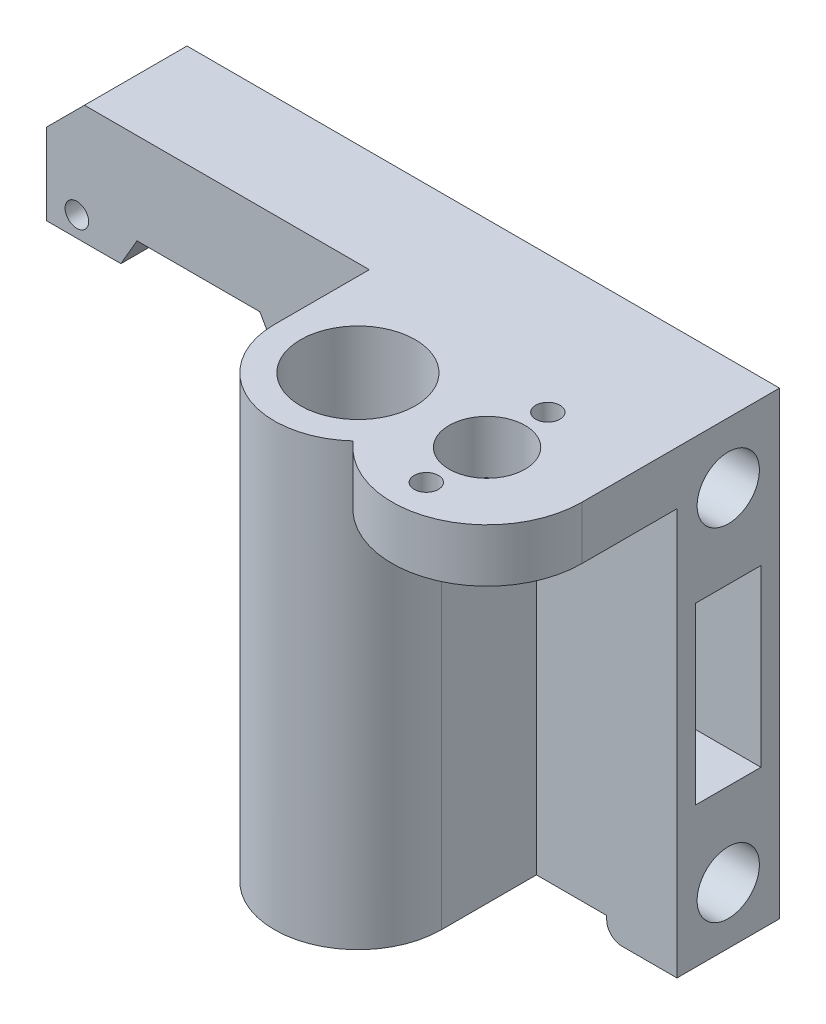
SolidWorks part; units mm, degrees
ref_plane "Alzado" through (0, 0, 0) normal (0, 0, 1) x (1, 0, 0)
ref_plane "Planta" through (0, 0, 0) normal (0, 1, 0) x (1, 0, 0)
ref_plane "Vista lateral" through (0, 0, 0) normal (1, 0, 0) x (0, 0, -1)
sketch "Croquis1" plane through (0, 0, 0) normal (0, 1, 0) x (1, 0, 0)
  line L0 (-11, 0) -> (-11, 12.5)
  line L2 (29.5, 0) -> (29.5, 8)
  line L4 (29.5, 8) -> (29.5, 26)
  line L5 (29.5, 26) -> (-53.5, 26)
  line L6 (-53.5, 26) -> (-53.5, 12.5)
  line L7 (-11, 12.5) -> (-53.5, 12.5)
  arc A0 (-11, 0) -> (7.4632, -8.0808) centre (0, 0) ccw
  arc A1 (7.4632, -8.0808) -> (29.5, 0) centre (17, 0) ccw
  circle A4 centre (0, 0) radius 7.55
  circle A5 centre (17, 0) radius 5
  dimension "D2" = 15.1
  dimension "D3" = 10
  dimension "D4" = 11
  dimension "D5" = 12.5
  dimension "D1" = 17
  dimension "D6" = 18
  dimension "D7" = 83
  dimension "D8" = 26
  dimension "D9" = 12.5
  dimension "D10" = 29.5
  dimension "D11" = 12.5
extrude "Saliente-Extruir1" add sketch "Croquis1" along normal blind 7
sketch "Croquis2" plane through (0, 0, 0) normal (0, -1, 0) x (1, 0, 0)
  line L0 (29.5, 0) -> (29.5, -26) construction
  line L1 (29.5, -26) -> (-53.5, -26) construction
  line L2 (-53.5, -12.5) -> (-11, -12.5) construction
  line L3 (-53.5, -26) -> (-53.5, -12.5) construction
  line L4 (29.5, 0) -> (29.5, -26)
  line L5 (29.5, -26) -> (-53.5, -26)
  line L6 (-53.5, -12.5) -> (-11, -12.5)
  line L7 (-53.5, -26) -> (-53.5, -12.5)
  line L8 (-11, -12.5) -> (29.5, -12.5)
  line M3 (-11, -12.5) -> (-53.5, -12.5)
  line M4 (-53.5, -12.5) -> (-53.5, -26)
  line M5 (-53.5, -26) -> (29.5, -26)
  line M6 (29.5, -26) -> (29.5, 0)
extrude "Saliente-Extruir2" add sketch "Croquis2" along normal blind 51 contours L8 M3 M4 M5 M6
sketch "Croquis3" plane through (0, 0, 0) normal (0, -1, 0) x (1, 0, 0)
  line L0 (-11, -12.5) -> (29.5, -12.5) construction
  line L1 (-11, -12.5) -> (-11, 0) construction
  line L2 (-11, -12.5) -> (11, -12.5)
  line L3 (-11, -12.5) -> (-11, 0)
  line L4 (11, 0) -> (11, -12.5)
  circle A0 centre (0, 0) radius 7.55 construction
  arc A1 (7.4632, 8.0808) -> (-11, 0) centre (0, 0) ccw construction
  circle A2 centre (0, 0) radius 7.55
  arc A3 (7.4632, 8.0808) -> (-11, 0) centre (0, 0) ccw
  arc A4 (11, 0) -> (-11, 0) centre (0, 0) ccw
  line M1 (-11, 0) -> (-11, -12.5)
  line M2 (-11, -12.5) -> (29.5, -12.5)
  arc M5 (7.4632, 8.0808) -> (-11, 0) centre (0, 0) ccw
  circle M6 centre (0, 0) radius 7.55
extrude "Saliente-Extruir3" add sketch "Croquis3" along normal blind 51 contours L4 A4 M5 M1 M2 M6
sketch "Croquis5" plane through (0, 0, -12.5) normal (0, 0, 1) x (1, 0, 0)
  line L0 (-53.5, 7) -> (-11, 7) construction
  line L1 (-53.5, 7) -> (-53.5, -51) construction
  line L2 (-53.5, 7) -> (-48.5, 7)
  line L3 (-53.5, 7) -> (-53.5, 2)
  line L4 (-53.5, 2) -> (-48.5, 7)
  dimension "D1" = 5
  dimension "D2" = 5
extrude "Cortar-Extruir2" cut sketch "Croquis5" against normal through all
sketch "Croquis7" plane through (29.5, 0, 0) normal (1, 0, 0) x (0, 0, -1)
  line L0 (0, 7) -> (26, 7) construction
  line L1 (26, 7) -> (26, -51) construction
  circle A0 centre (19.25, -1) radius 4.1
  circle A1 centre (19.25, -46) radius 4.1
  dimension "D1" = 8.2
  dimension "D2" = 8.2
  dimension "D3" = 45
  dimension "D4" = 8
  dimension "D5" = 6.75
extrude "Cortar-Extruir3" cut sketch "Croquis7" against normal blind 35
sketch "Croquis8" plane through (29.5, 0, 0) normal (1, 0, 0) x (0, 0, -1)
  line L0 (12.5, -51) -> (12.5, 0) construction
  line L1 (14.95, -12) -> (23.55, -12)
  line L2 (14.95, -12) -> (14.95, -35)
  line L3 (14.95, -35) -> (23.55, -35)
  line L4 (23.55, -12) -> (23.55, -35)
  line L5 (14.95, -12) -> (23.55, -35) construction
  line L6 (14.95, -35) -> (23.55, -12) construction
  circle A0 centre (19.25, -1) radius 4.1 construction
  point P0 (19.25, -23.5)
  dimension "D1" = 8.6
  dimension "D2" = 23
  dimension "D3" = 6.75
  dimension "D4" = 22.5
extrude "Cortar-Extruir4" cut sketch "Croquis8" against normal through all
sketch "Croquis10" plane through (0, 0, -12.5) normal (0, 0, 1) x (1, 0, 0)
  line L0 (-53.5, 2) -> (-53.5, -51) construction
  line L1 (-48.5, 7) -> (-11, 7) construction
  circle A0 centre (-49.5, -6) radius 1.55
  circle A1 centre (-18.5, -6) radius 1.55
  circle A2 centre (-18.5, -37) radius 1.55
  circle A3 centre (-34, -21.5) radius 11 construction
  point P9 (-53.5, -24.5)
  dimension "D3" = 3.1
  dimension "D4" = 3.1
  dimension "D5" = 3.1
  dimension "D8" = 22
  dimension "D1" = 31
  dimension "D2" = 31
  dimension "D6" = 4
  dimension "D7" = 13
  dimension "D9" = 15.5
  dimension "D10" = 15.5
extrude "Cortar-Extruir7" cut sketch "Croquis10" against normal through all
sketch "Croquis11" plane through (0, 0, -12.5) normal (0, 0, 1) x (1, 0, 0)
  line L0 (-53.5, 2) -> (-53.5, -51) construction
  line L1 (-53.5, -8.6693) -> (-53.5, -51)
  line L2 (-53.5, -8.6693) -> (-43.7014, -8.6693)
  line L4 (-25.4171, -33) -> (-17.3342, -19)
  line L5 (-17.3342, -19) -> (-25.4171, -5)
  line L6 (-25.4171, -5) -> (-41.5829, -5)
  line L7 (-41.5829, -5) -> (-43.7014, -8.6693)
  line L8 (-25.4171, -33) -> (-25.4171, -51)
  line L9 (-25.4171, -51) -> (-53.5, -51)
  line L10 (-53.5, -51) -> (-53.5, -8.6693)
  line L11 (-49.6658, -19) -> (-45.6244, -26) [skipped]
  line L12 (-41.5829, -33) -> (-25.4171, -33) [skipped]
  arc A0 (-21.3756, -26) -> (-33.5, -5) centre (-33.5, -19) ccw construction
  line M9 (-53.5, 2) -> (-53.5, -51)
  dimension "D1" = 28
  dimension "D2" = 20
  dimension "D3" = 32
  dimension "D4" = 9.7986
  dimension "D5" = 18
  dimension "D6" = 28.0829
extrude "Cortar-Extruir8" cut sketch "Croquis11" against normal through all contours L9 L8 L4 L5 L6 L7 L2 M9
sketch "Croquis12" plane through (0, 0, -12.5) normal (0, 0, 1) x (1, 0, 0)
  line L0 (-25.4171, -51) -> (-25.4171, -46)
  line L1 (-25.4171, -33) -> (-25.4171, -51) construction
  line L2 (-25.4171, -46) -> (-11, -46)
  line L3 (-11, 7) -> (-11, -51) construction
  line L4 (-11, -46) -> (-11, -51)
  line L5 (-25.4171, -51) -> (-11, -51) construction
  line L6 (-11, -51) -> (-25.4171, -51)
  dimension "D1" = 5
extrude "Cortar-Extruir9" cut sketch "Croquis12" against normal through all
sketch "Croquis13" plane through (0, -51, 0) normal (0, -1, 0) x (1, 0, 0)
  line L0 (29.5, -12.5) -> (20.25, -12.5)
  line L1 (11, -12.5) -> (29.5, -12.5) construction
  line L2 (20.25, -12.5) -> (20.25, -26)
  line L3 (-11, -26) -> (29.5, -26) construction
  line L4 (20.25, -26) -> (29.5, -26)
  line L5 (29.5, -26) -> (29.5, -12.5)
extrude "Saliente-Extruir4" add sketch "Croquis13" along normal blind 2.5
fillet "Redondeo2" radius 2 1 edges at (20.25, -53.5, -19.25)
sketch "Croquis14" plane through (0, -53.5, 0) normal (0, -1, 0) x (1, 0, 0)
  line L0 (29.5, -12.5) -> (22.25, -12.5) construction
  line L1 (22.25, -12.5) -> (22.25, -26) construction
  circle A0 centre (24.25, -14) radius 1
  circle A1 centre (24.25, -24) radius 1
  dimension "D1" = 2
  dimension "D2" = 2
  dimension "D3" = 10
  dimension "D4" = 1.5
  dimension "D5" = 2
extrude "Cortar-Extruir10" cut sketch "Croquis14" against normal blind 4
sketch "Croquis15" plane through (0, 7, 0) normal (0, 1, 0) x (1, 0, 0)
  circle A0 centre (17, 0) radius 5 construction
  circle A1 centre (17, 0) radius 5 construction
  circle A2 centre (17, 0) radius 8 construction
  circle A3 centre (17, 8) radius 1.6
  circle A4 centre (17, -8) radius 1.6
  dimension "D1" = 16
  dimension "D2" = 3.2
  dimension "D3" = 3.2
extrude "Cortar-Extruir11" cut sketch "Croquis15" against normal through all
